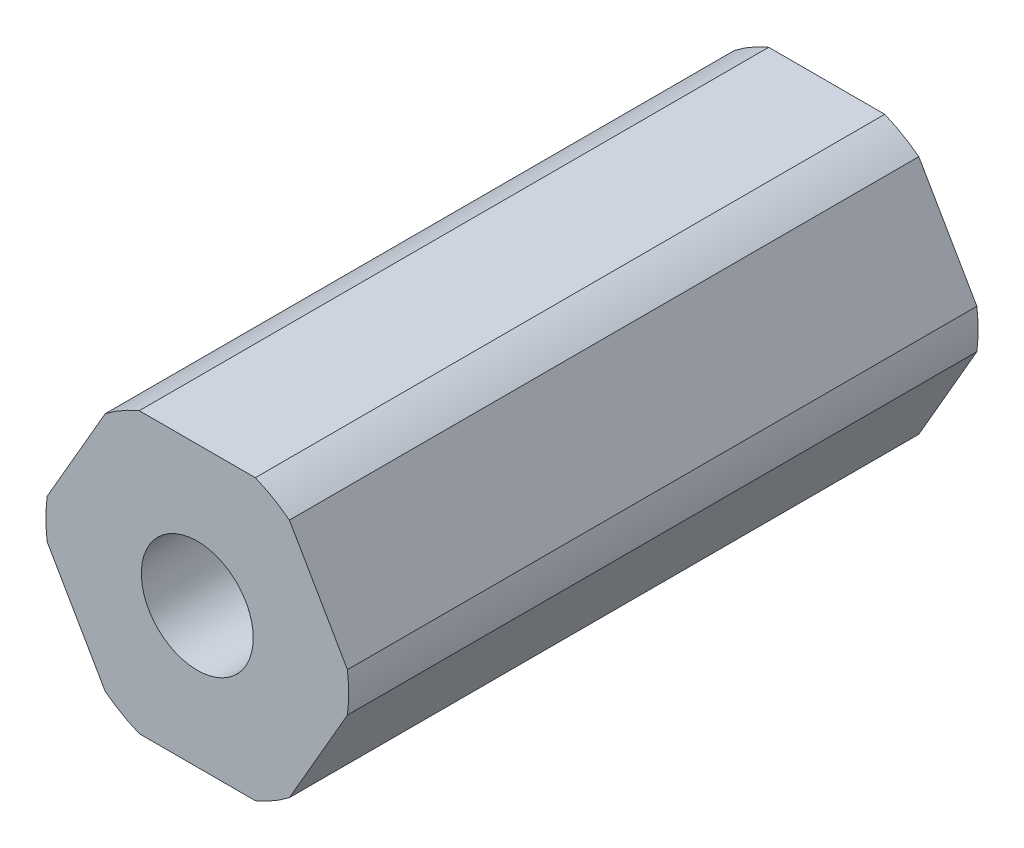
SolidWorks part; units mm, degrees
ref_plane "Front Plane" through (0, 0, 0) normal (0, 0, 1) x (1, 0, 0)
ref_plane "Top Plane" through (0, 0, 0) normal (0, 1, 0) x (1, 0, 0)
ref_plane "Right Plane" through (0, 0, 0) normal (1, 0, 0) x (0, 0, -1)
sketch "Sketch1" plane through (0, 0, 0) normal (0, 0, 1) x (1, 0, 0)
  line L1 (4.1818, -5.457) -> (6.8168, -0.893)
  line L2 (6.8168, 0.893) -> (4.1818, 5.457)
  line L3 (2.635, 6.35) -> (-2.635, 6.35)
  line L4 (-4.1818, 5.457) -> (-6.8168, 0.893)
  line L5 (-6.8168, -0.893) -> (-4.1818, -5.457)
  line L6 (-2.635, -6.35) -> (2.635, -6.35)
  arc A0 (-2.635, 6.35) -> (-4.1818, 5.457) centre (0, 0) ccw
  circle A1 centre (0, 0) radius 6.35 construction
  arc A2 (4.1818, 5.457) -> (2.635, 6.35) centre (0, 0) ccw
  arc A3 (6.8168, -0.893) -> (6.8168, 0.893) centre (0, 0) ccw
  arc A4 (2.635, -6.35) -> (4.1818, -5.457) centre (0, 0) ccw
  arc A5 (-4.1818, -5.457) -> (-2.635, -6.35) centre (0, 0) ccw
  arc A6 (-6.8168, 0.893) -> (-6.8168, -0.893) centre (0, 0) ccw
  circle A7 centre (0, 0) radius 2.54
  dimension "D1" = 12.7
  dimension "D2" = 13.75
  dimension "D3" = 5.08
extrude "Boss-Extrude1" add sketch "Sketch1" along normal blind 28.575
